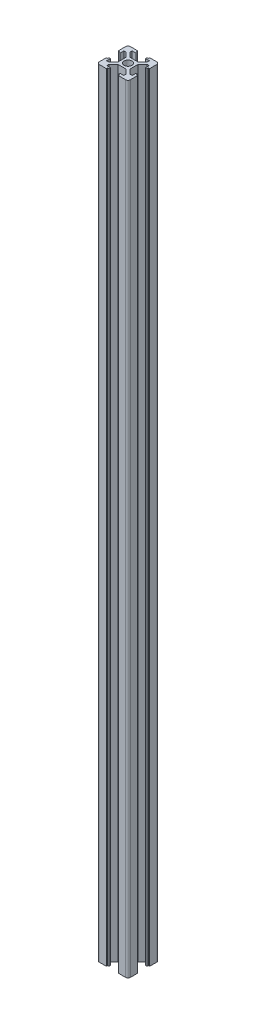
SolidWorks part; units mm, degrees
material "6063-O"
ref_plane "Front Plane" through (0, 0, 0) normal (0, 0, 1) x (1, 0, 0)
ref_plane "Top Plane" through (0, 0, 0) normal (0, 1, 0) x (1, 0, 0)
ref_plane "Right Plane" through (0, 0, 0) normal (1, 0, 0) x (0, 0, -1)
sketch "Sketch1" plane through (0, 0, 0) normal (0, 1, 0) x (1, 0, 0)
  line L0 (0, 14.5399) -> (0, 10) construction
  line L1 (-16.8658, 0) -> (2.5, 0) construction
  line L2 (13.2784, 3.9) -> (3.9, 3.9) construction
  line L3 (0, 0) -> (2.5, 0)
  line L4 (0, 0) -> (0, 2.5)
  line L5 (3.9, 10) -> (8.5, 10)
  line L6 (9.2, 0) -> (16.4291, 0) construction
  line L7 (-2.63, 3.9) -> (2.63, 3.9)
  line L9 (2.5491, 3.9) -> (2.63, 3.9)
  line L10 (3.9, 0) -> (3.9, 2.63)
  line L11 (13.2784, 3.1) -> (2.5491, 3.1) construction
  line L12 (8.2, 7.5573) -> (8.2, -3.0868) construction
  line L13 (9.2, 7.2593) -> (9.2, -8.1534) construction
  line L14 (10, 3.9) -> (9.2, 3.9)
  line L15 (9.2, 3.9) -> (9.2, 3.1)
  line L16 (9.2, 3.1) -> (8.2, 3.1)
  line L17 (8.2, 3.1) -> (8.2, 5.5)
  line L18 (8.2, 5.5) -> (6.77, 5.5)
  line L19 (6.77, 5.5) -> (3.9, 2.63)
  line L20 (5.0973, 5.5) -> (13.0082, 5.5) construction
  line L21 (3.1, 11.2046) -> (3.1, 2.6994) construction
  line L22 (3.9, 10.7498) -> (3.9, 3.9) construction
  line L23 (5.5, 11.523) -> (5.5, 1.4941) construction
  line L24 (-2.2597, 8.2) -> (6.1545, 8.2) construction
  line L25 (-2.9419, 9.2) -> (5.7225, 9.2) construction
  line L26 (3.9, 10) -> (3.9, 9.2)
  line L27 (3.9, 9.2) -> (3.1, 9.2)
  line L28 (3.1, 9.2) -> (3.1, 8.2)
  line L29 (3.1, 8.2) -> (5.5, 8.2)
  line L30 (5.5, 8.2) -> (5.5, 6.77)
  line L31 (5.5, 6.77) -> (2.63, 3.9)
  line L32 (0, 2.5) -> (0, -14.4122) construction
  line L33 (10, 3.9) -> (10, 8.5)
  line L34 (9.2, 0) -> (10, 0)
  line L35 (2.63, 3.9) -> (2.5491, 3.9) construction
  line L36 (3.9, 2.63) -> (3.9, 2.0627) construction
  line L37 (10, -3.9) -> (10, -8.5)
  line L38 (3.9, -10) -> (8.5, -10)
  line L39 (3.9, -10) -> (3.9, -9.2)
  line L40 (3.9, -9.2) -> (3.1, -9.2)
  line L41 (3.1, -9.2) -> (3.1, -8.2)
  line L42 (3.1, -8.2) -> (5.5, -8.2)
  line L43 (5.5, -8.2) -> (5.5, -6.77)
  line L44 (5.5, -6.77) -> (2.63, -3.9)
  line L45 (0, -3.9) -> (2.63, -3.9)
  line L46 (3.9, 0) -> (3.9, -2.63)
  line L47 (6.77, -5.5) -> (3.9, -2.63)
  line L48 (8.2, -5.5) -> (6.77, -5.5)
  line L49 (8.2, -3.1) -> (8.2, -5.5)
  line L50 (9.2, -3.1) -> (8.2, -3.1)
  line L51 (9.2, -3.9) -> (9.2, -3.1)
  line L52 (10, -3.9) -> (9.2, -3.9)
  line L53 (-3.9, -10) -> (-8.5, -10)
  line L54 (-10, -3.9) -> (-10, -8.5)
  line L55 (-10, -3.9) -> (-9.2, -3.9)
  line L56 (-9.2, -3.9) -> (-9.2, -3.1)
  line L57 (-9.2, -3.1) -> (-8.2, -3.1)
  line L58 (-8.2, -3.1) -> (-8.2, -5.5)
  line L59 (-8.2, -5.5) -> (-6.77, -5.5)
  line L60 (-6.77, -5.5) -> (-3.9, -2.63)
  line L61 (-3.9, 0) -> (-3.9, -2.63)
  line L62 (0, -3.9) -> (-2.63, -3.9)
  line L63 (-5.5, -6.77) -> (-2.63, -3.9)
  line L64 (-5.5, -8.2) -> (-5.5, -6.77)
  line L65 (-3.1, -8.2) -> (-5.5, -8.2)
  line L66 (-3.1, -9.2) -> (-3.1, -8.2)
  line L67 (-3.9, -9.2) -> (-3.1, -9.2)
  line L68 (-3.9, -10) -> (-3.9, -9.2)
  line L69 (-10, 3.9) -> (-10, 8.5)
  line L70 (-3.9, 10) -> (-8.5, 10)
  line L71 (-3.9, 10) -> (-3.9, 9.2)
  line L72 (-3.9, 9.2) -> (-3.1, 9.2)
  line L73 (-3.1, 9.2) -> (-3.1, 8.2)
  line L74 (-3.1, 8.2) -> (-5.5, 8.2)
  line L75 (-5.5, 8.2) -> (-5.5, 6.77)
  line L76 (-5.5, 6.77) -> (-2.63, 3.9)
  line L78 (-3.9, 0) -> (-3.9, 2.63)
  line L79 (-6.77, 5.5) -> (-3.9, 2.63)
  line L80 (-8.2, 5.5) -> (-6.77, 5.5)
  line L81 (-8.2, 3.1) -> (-8.2, 5.5)
  line L82 (-9.2, 3.1) -> (-8.2, 3.1)
  line L83 (-9.2, 3.9) -> (-9.2, 3.1)
  line L84 (-10, 3.9) -> (-9.2, 3.9)
  line L85 (0, 3.9) -> (-2.63, 3.9) [skipped]
  circle A0 centre (0, 0) radius 2.5
  arc A1 (8.5, 10) -> (10, 8.5) centre (8.5, 8.5) cw
  arc A2 (10, -8.5) -> (8.5, -10) centre (8.5, -8.5) cw
  arc A4 (-8.5, -10) -> (-10, -8.5) centre (-8.5, -8.5) cw
  arc A6 (-10, 8.5) -> (-8.5, 10) centre (-8.5, 8.5) cw
  point P12 (10, 10)
  point P126 (0, 0)
  dimension "D3" = 5
  dimension "D4" = 1.5
  dimension "D1" = 10
  dimension "D2" = 10
  dimension "D6" = 3.9
  dimension "D7" = 3.9
  dimension "D8" = 3.1
  dimension "D9" = 4
  dimension "D11" = 5.5
  dimension "D12" = 1.8
  dimension "D13" = 0.8
  dimension "D14" = 3.9
  dimension "D15" = 3.1
  dimension "D16" = 5.5
  dimension "D17" = 1.27
  dimension "D18" = 1.27
  dimension "D19" = 1.27
  dimension "D20" = 1.27
extrude "Boss-Extrude1" add sketch "Sketch1" along normal blind 500 contours A6 L69 L84 L83 L82 L81 L80 L79 L78 L61 L60 L59 L58 L57 L56 L55 L54 A4 L53 L68 L67 L66 L65 L64 L63 L62 L45 L44 L43 L42 L41 L40 L39 L38 A2 L37 L52 L51 L50 L49 L48 L47 L46 L10 L19 L18 L17 L16 L15 L14 L33
